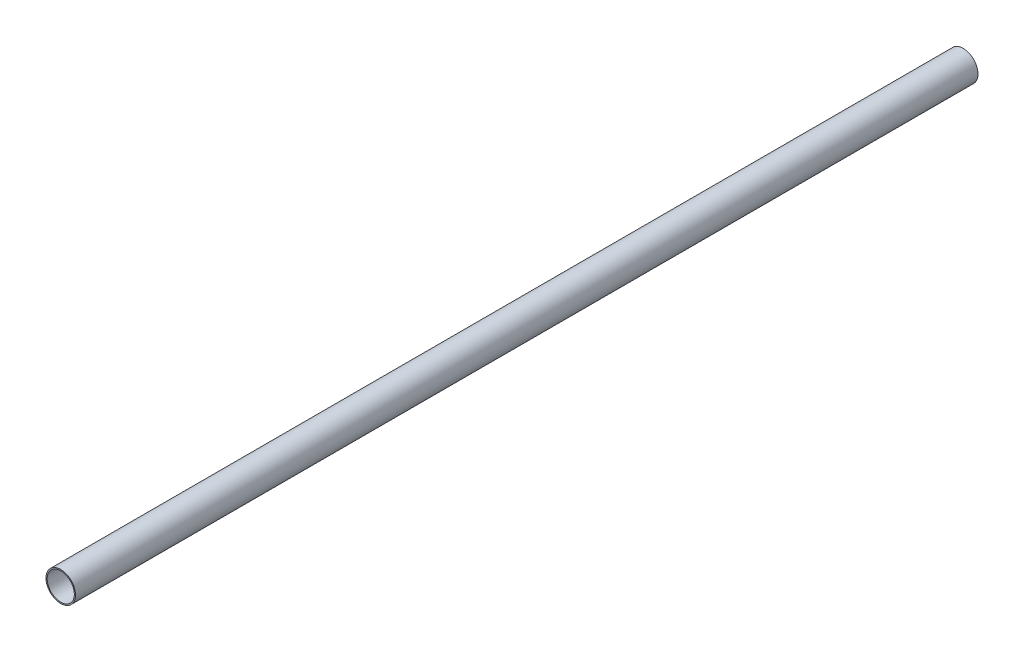
SolidWorks part; units mm, degrees
ref_plane "Front Plane" through (0, 0, 0) normal (0, 0, 1) x (1, 0, 0)
ref_plane "Top Plane" through (0, 0, 0) normal (0, 1, 0) x (1, 0, 0)
ref_plane "Right Plane" through (0, 0, 0) normal (1, 0, 0) x (0, 0, -1)
sketch "Sketch1" plane through (0, 0, 0) normal (0, 0, 1) x (1, 0, 0)
  line L0 (13.716, 0) -> (12.6238, 0) construction
  circle A0 centre (0, 0) radius 13.716
  circle A1 centre (0, 0) radius 12.6238 construction
  dimension "Dia." = 27.432
  dimension "Wall Thick." = 1.0922
extrude "Extrude-Thin1" add sketch "Sketch1" along normal mid plane 838.2 thin thin type one direction reverse wall 1.0922
equation "\"D5@Extrude-Thin1\" = \"Wall Thick.@Sketch1\""
